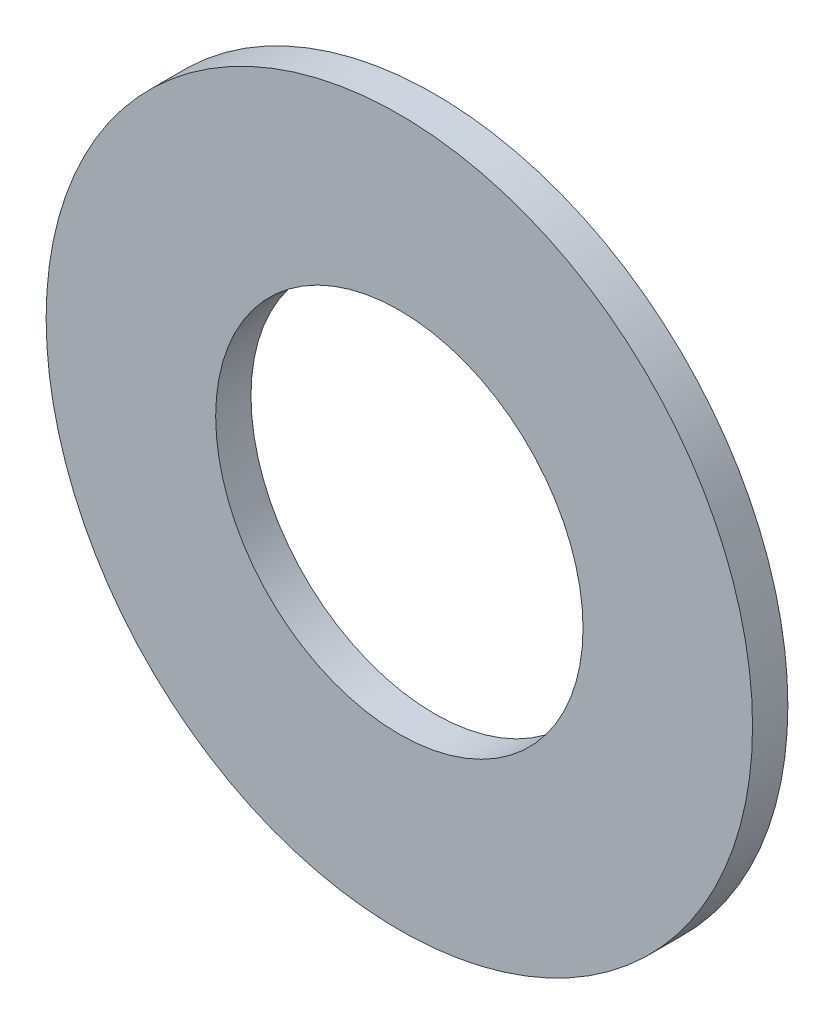
SolidWorks part; units mm, degrees
ref_plane "前视基准面" through (0, 0, 0) normal (0, 0, 1) x (1, 0, 0)
ref_plane "上视基准面" through (0, 0, 0) normal (0, 1, 0) x (1, 0, 0)
ref_plane "右视基准面" through (0, 0, 0) normal (1, 0, 0) x (0, 0, -1)
other "Configuration Table"
sketch "草图1" plane through (0, 0, 0) normal (0, 0, 1) x (1, 0, 0)
  circle A0 centre (0, 0) radius 2.6
  circle A1 centre (0, 0) radius 5
  dimension "D1" = 5.2
  dimension "D2" = 10
extrude "凸台-拉伸1" add sketch "草图1" along normal blind 0.5
